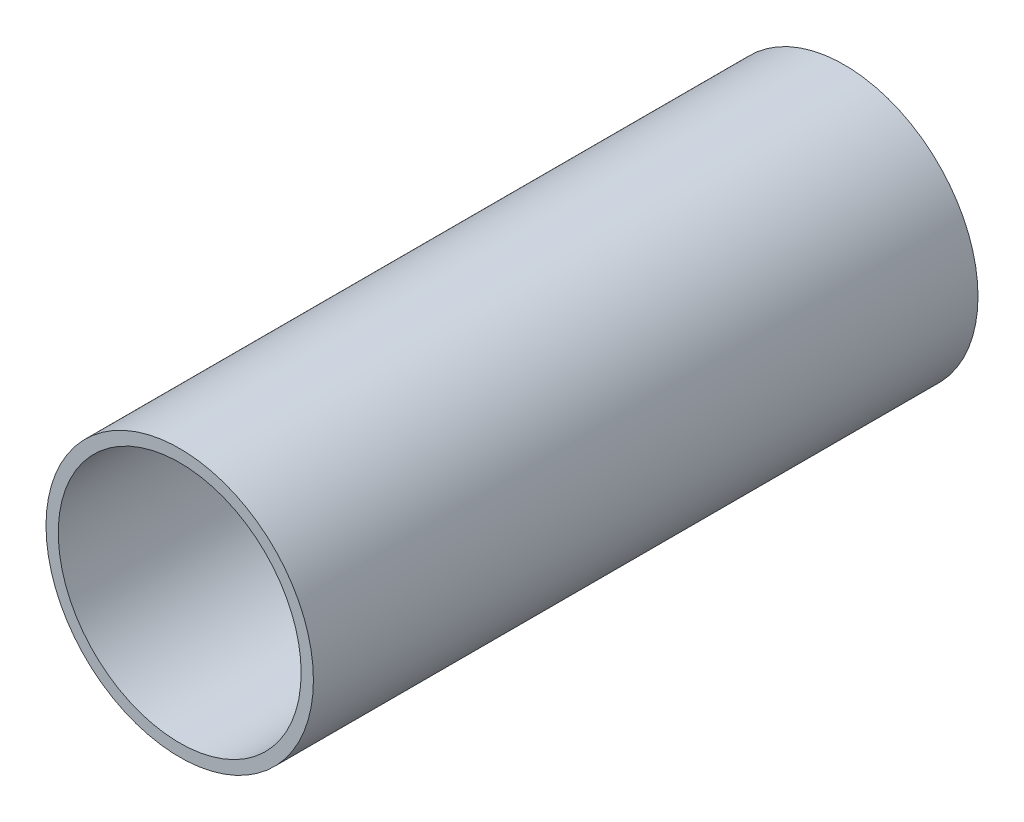
SolidWorks part; units mm, degrees
ref_plane "Front Plane" through (0, 0, 0) normal (0, 0, 1) x (1, 0, 0)
ref_plane "Top Plane" through (0, 0, 0) normal (0, 1, 0) x (1, 0, 0)
ref_plane "Right Plane" through (0, 0, 0) normal (1, 0, 0) x (0, 0, -1)
sketch "Sketch2" plane through (0, 0, 0) normal (0, 0, 1) x (1, 0, 0)
  circle A0 centre (0, 0) radius 84.5
  circle A1 centre (0, 0) radius 76.75
  dimension "D1" = 169
  dimension "D2" = 153.5
extrude "Boss-Extrude1" add sketch "Sketch2" along normal blind 420
